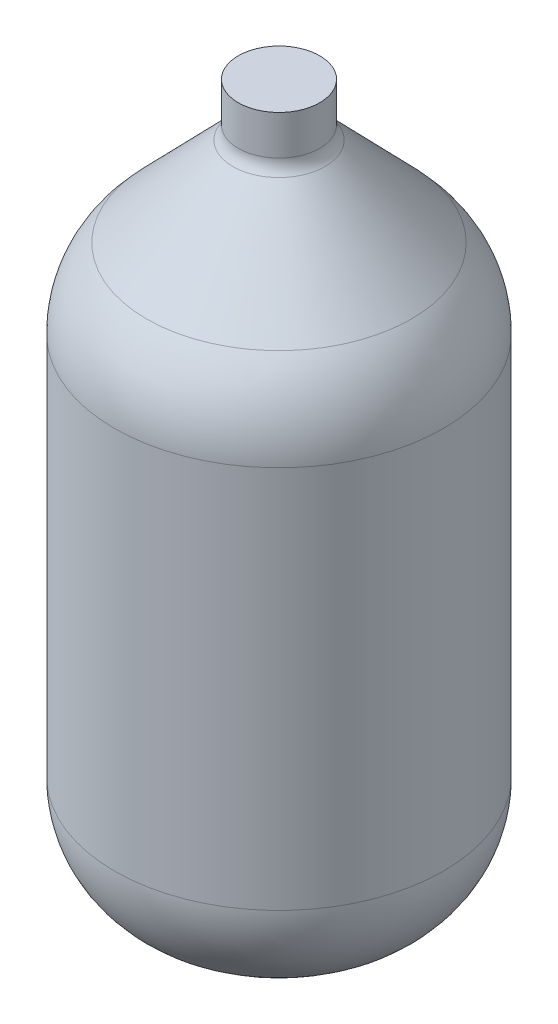
SolidWorks part; units mm, degrees
ref_plane "Front Plane" through (0, 0, 0) normal (0, 0, 1) x (1, 0, 0)
ref_plane "Top Plane" through (0, 0, 0) normal (0, 1, 0) x (1, 0, 0)
ref_plane "Right Plane" through (0, 0, 0) normal (1, 0, 0) x (0, 0, -1)
sketch "Sketch4" plane through (0, 0, 0) normal (1, 0, 0) x (0, 0, -1)
  line L0 (-55.372, 0) -> (55.372, 0) construction
  line L1 (55.372, 64.5609) -> (55.372, -64.5609)
  line L2 (13.716, 138.7623) -> (-13.716, 138.7623) construction
  line L3 (13.716, 138.7623) -> (13.716, 125.4646)
  line L4 (15.5122, 121.039) -> (44.5946, 91.1144)
  line L5 (38.2459, -96.3682) -> (20.9739, -107.7575)
  line L6 (0, 138.7623) -> (0, -114.0501)
  line L7 (-38.2459, -96.3682) -> (-20.9739, -107.7575) construction
  line L8 (0, -114.0501) -> (0, -121.5877) construction
  line L9 (13.716, 138.7623) -> (0, 138.7623)
  arc A0 (55.372, -64.5609) -> (38.2459, -96.3682) centre (17.272, -64.5609) cw
  arc A1 (55.372, 64.5609) -> (44.5946, 91.1144) centre (17.272, 64.5609) ccw
  arc A2 (0, -114.0501) -> (20.9739, -107.7575) centre (0, -75.9501) ccw
  arc A3 (-20.9739, -107.7575) -> (0, -114.0501) centre (0, -75.9501) ccw construction
  arc A4 (13.716, 125.4646) -> (15.5122, 121.039) centre (20.066, 125.4646) ccw
  point P2 (0, 0)
  point P6 (55.372, 0)
  point P9 (0, 138.7623)
  point P10 (0, -121.5877)
  point P16 (55.372, -85.0752)
  point P19 (55.372, 80.0248)
  point P27 (13.716, 122.8873)
  dimension "D7" = 38.1
  dimension "D8" = 38.1
  dimension "D9" = 6.35
  dimension "D1" = 110.744
  dimension "D2" = 165.1
  dimension "D3" = 260.35
  dimension "D4" = 36.5125
  dimension "D5" = 27.432
  dimension "D6" = 15.875
revolve "Revolve3" add sketch "Sketch4" angle 360 about L6
